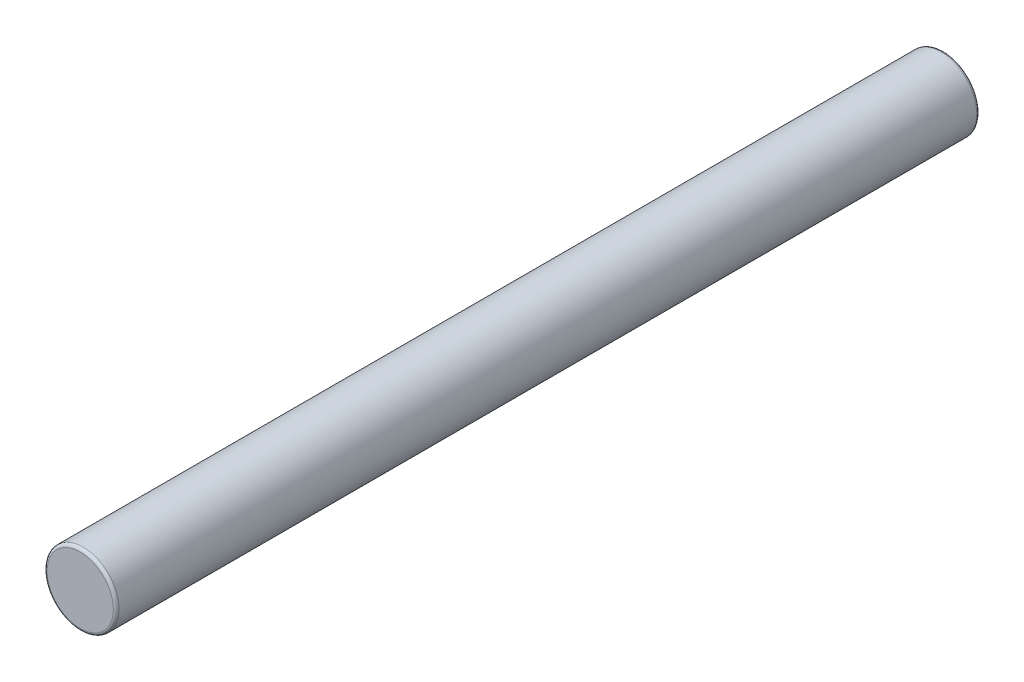
SolidWorks part; units mm, degrees
ref_plane "Front Plane" through (0, 0, 0) normal (0, 0, 1) x (1, 0, 0)
ref_plane "Top Plane" through (0, 0, 0) normal (0, 1, 0) x (1, 0, 0)
ref_plane "Right Plane" through (0, 0, 0) normal (1, 0, 0) x (0, 0, -1)
sketch "Sketch1" plane through (0, 0, 0) normal (0, 0, 1) x (1, 0, 0)
  circle A0 centre (0, 0) radius 2.5
extrude "Boss-Extrude1" add sketch "Sketch1" along normal blind 60
fillet "Fillet1" radius 0.2 2 edges at (2.5, 0, 0) (2.5, 0, 60)
